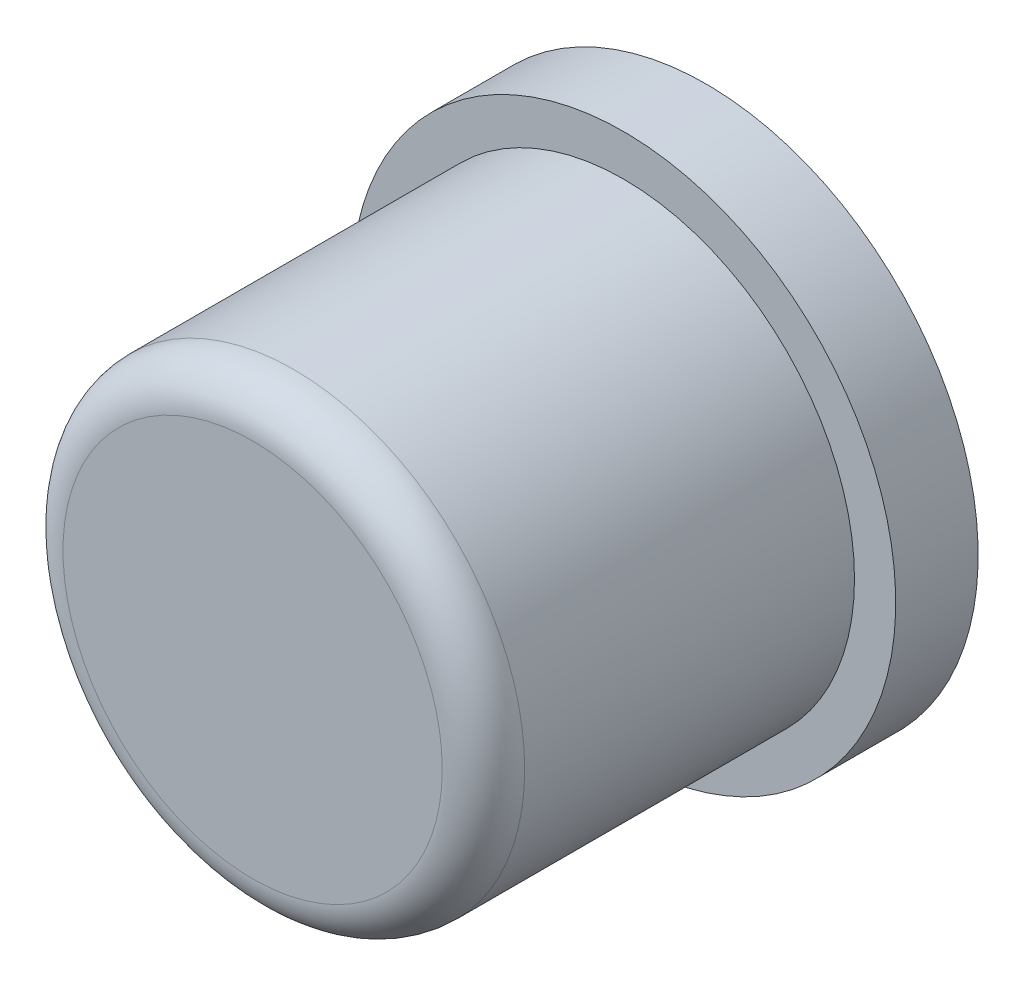
SolidWorks part; units mm, degrees
ref_plane "Front Plane" through (0, 0, 0) normal (0, 0, 1) x (1, 0, 0)
ref_plane "Top Plane" through (0, 0, 0) normal (0, 1, 0) x (1, 0, 0)
ref_plane "Right Plane" through (0, 0, 0) normal (1, 0, 0) x (0, 0, -1)
sketch "草图1" plane through (0, 0, 0) normal (0, 0, 1) x (1, 0, 0)
  circle A0 centre (0, 0) radius 2.8
  dimension "D1" = 5.6
extrude "凸台-拉伸1" add sketch "草图1" along normal blind 5.5
sketch "草图2" plane through (0, 0, 0) normal (0, 0, -1) x (-1, 0, 0)
  circle A0 centre (0, 0) radius 3.3
extrude "凸台-拉伸2" add sketch "草图2" against normal blind 1 contours A0
sketch "草图3" plane through (0, 0, 0) normal (0, 0, -1) x (-1, 0, 0)
  circle A0 centre (0, 0) radius 2
  dimension "D1" = 4
extrude "切除-拉伸1" cut sketch "草图3" against normal blind 0.5
fillet "圆角1" radius 0.5 1 edges at (2.8, 0, 5.5)
